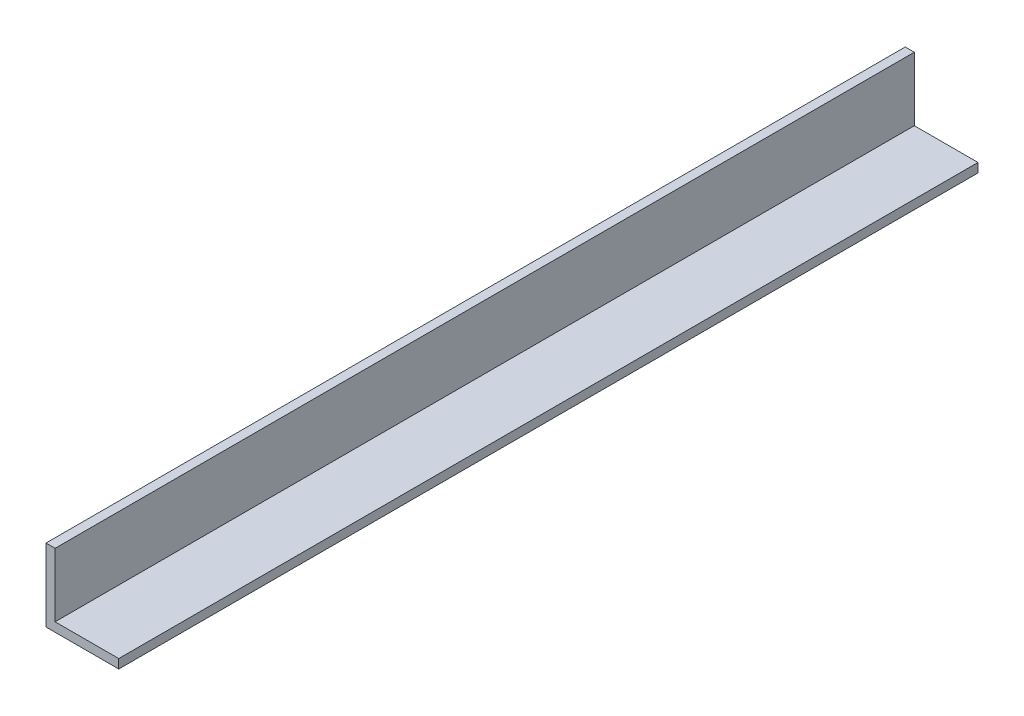
SolidWorks part; units mm, degrees
ref_plane "Front Plane" through (0, 0, 0) normal (0, 0, 1) x (1, 0, 0)
ref_plane "Top Plane" through (0, 0, 0) normal (0, 1, 0) x (1, 0, 0)
ref_plane "Right Plane" through (0, 0, 0) normal (1, 0, 0) x (0, 0, -1)
sketch "Sketch1" plane through (0, 0, 0) normal (0, 0, 1) x (1, 0, 0)
  line L0 (0, 25.4) -> (0, 0)
  line L1 (0, 0) -> (25.4, 0)
  line L2 (25.4, 0) -> (25.4, 3.175)
  line L3 (25.4, 3.175) -> (3.175, 3.175)
  line L4 (3.175, 3.175) -> (3.175, 25.4)
  line L5 (3.175, 25.4) -> (0, 25.4)
  dimension "D1" = 25.4
  dimension "D2" = 3.175
extrude "Boss-Extrude1" add sketch "Sketch1" along normal mid plane 300
